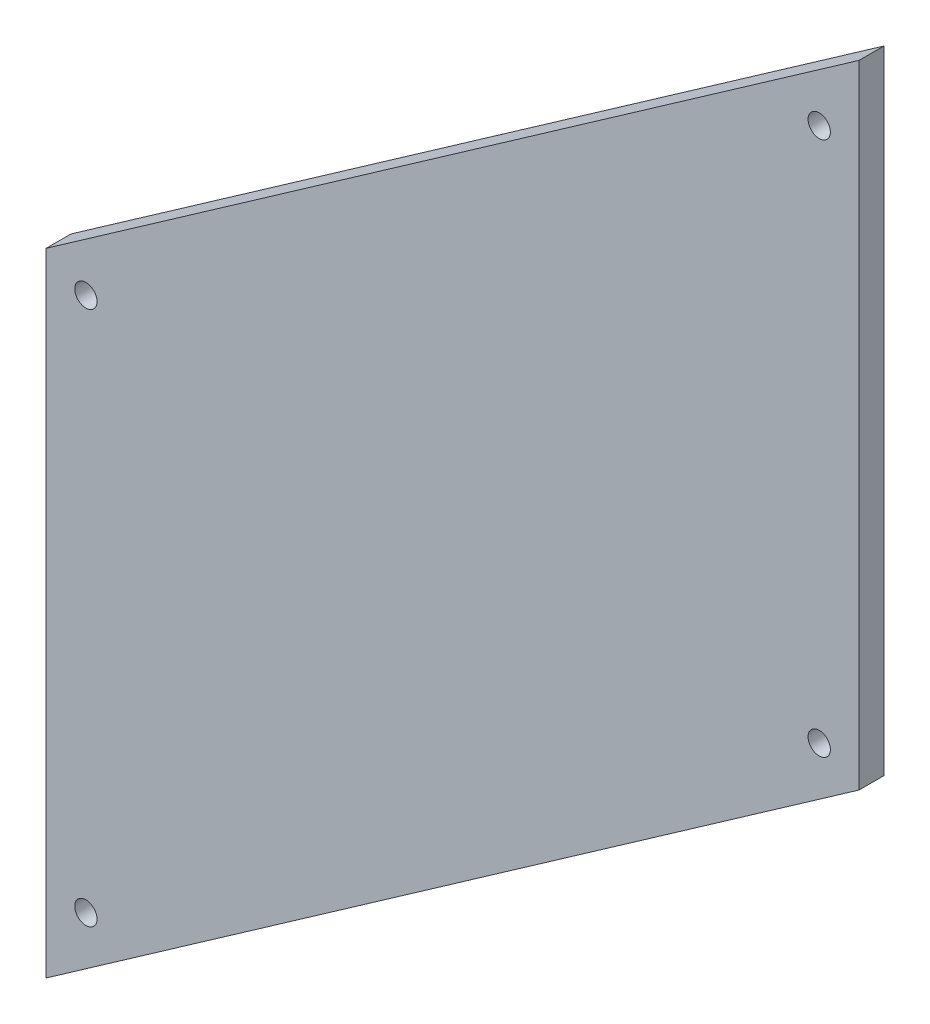
SolidWorks part; units mm, degrees
material "Pine"
ref_plane "Front Plane" through (0, 0, 0) normal (0, 0, 1) x (1, 0, 0)
ref_plane "Top Plane" through (0, 0, 0) normal (0, 1, 0) x (1, 0, 0)
ref_plane "Right Plane" through (0, 0, 0) normal (1, 0, 0) x (0, 0, -1)
sketch "Sketch1" plane through (0, 0, 0) normal (0, 0, 1) x (1, 0, 0)
  line L0 (0, 0) -> (0, 302.3248)
  line L1 (0, 302.3248) -> (388.9375, 574.6618)
  line L2 (388.9375, 574.6618) -> (388.9375, 272.337)
  line L3 (388.9375, 272.337) -> (0, 0)
  circle A0 centre (19.05, 292.408) radius 5.334
  circle A1 centre (19.05, 36.5947) radius 5.334
  circle A2 centre (369.8875, 282.2538) radius 5.334
  circle A3 centre (369.8875, 538.0671) radius 5.334
  dimension "D4" = 10.668
  dimension "D2" = 388.9375
  dimension "D3" = 55
  dimension "D5" = 19.05
  dimension "D6" = 19.05
  dimension "D7" = 19.05
  dimension "D8" = 19.05
  dimension "D9" = 19.05
  dimension "D10" = 19.05
  dimension "D11" = 247.65
extrude "Boss-Extrude1" add sketch "Sketch1" along normal blind 11.9062
